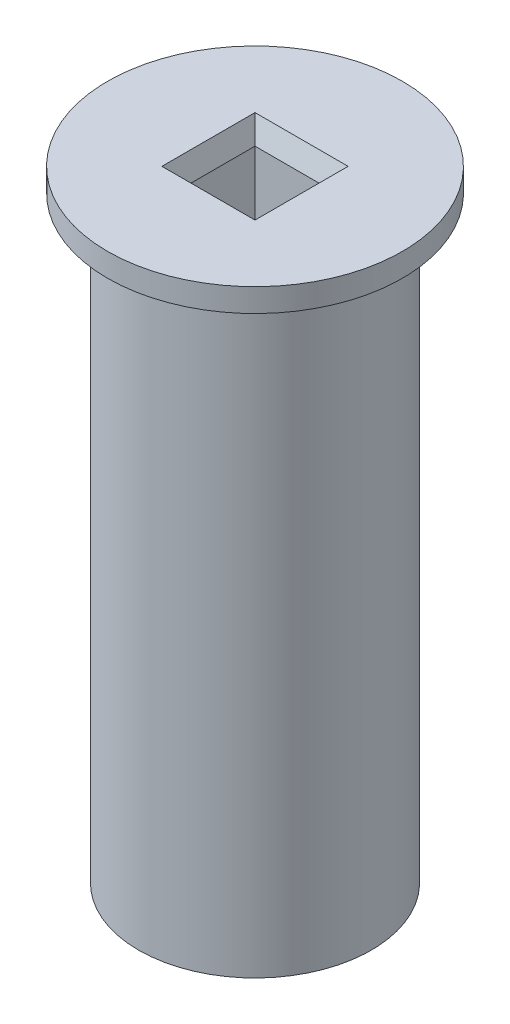
SolidWorks part; units mm, degrees
ref_plane "Спереди" through (0, 0, 0) normal (0, 0, 1) x (1, 0, 0)
ref_plane "Сверху" through (0, 0, 0) normal (0, 1, 0) x (1, 0, 0)
ref_plane "Справа" through (0, 0, 0) normal (1, 0, 0) x (0, 0, -1)
sketch "Эскиз1" plane through (0, 0, 0) normal (0, 1, 0) x (1, 0, 0)
  line L1 (5, -5) -> (-5, -5)
  line L2 (5, -5) -> (5, 5)
  line L3 (5, 5) -> (-5, 5)
  line L4 (-5, -5) -> (-5, 5)
  line L5 (5, -5) -> (-5, 5) construction
  line L6 (5, 5) -> (-5, -5) construction
  circle A0 centre (0, 0) radius 15
  dimension "D1" = 30
  dimension "D2" = 10
extrude "Бобышка-Вытянуть1" add sketch "Эскиз1" along normal blind 80
sketch "Sketch1" plane through (0, 80, 0) normal (0, 1, 0) x (1, 0, 0)
  line L1 (5, -5) -> (-5, -5)
  line L2 (5, -5) -> (5, 5)
  line L3 (5, 5) -> (-5, 5)
  line L4 (-5, -5) -> (-5, 5)
  line L5 (5, -5) -> (-5, 5) construction
  line L6 (5, 5) -> (-5, -5) construction
  circle A0 centre (0, 0) radius 19
  dimension "D1" = 38
extrude "Boss-Extrude1" add sketch "Sketch1" against normal blind 3
chamfer "Chamfer1" distance 1 angle 70 4 edges at (5, 80, 0) (0, 80, 5) (-5, 80, 0) (0, 80, -5)
